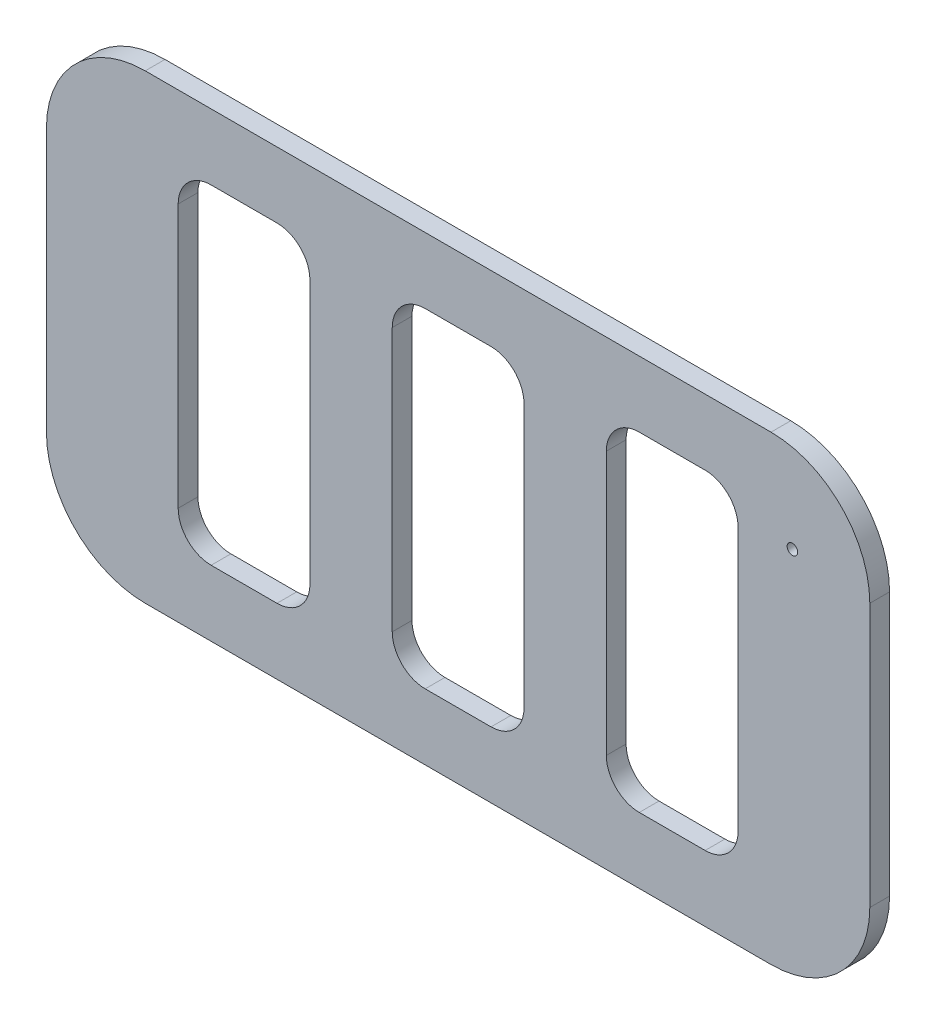
SolidWorks part; units mm, degrees
material "Ferro dúctil"
ref_plane "Plano frontal" through (0, 0, 0) normal (0, 0, 1) x (1, 0, 0)
ref_plane "Plano superior" through (0, 0, 0) normal (0, 1, 0) x (1, 0, 0)
ref_plane "Plano direito" through (0, 0, 0) normal (1, 0, 0) x (0, 0, -1)
sketch "Esboço1" plane through (0, 0, 0) normal (0, 0, 1) x (1, 0, 0)
  line L1 (4.5869, 67.2368) -> (99.5869, 67.2368)
  line L2 (-10.4131, 52.2368) -> (-10.4131, 12.2368)
  line L3 (4.5869, -2.7632) -> (99.5869, -2.7632)
  line L4 (114.5869, 52.2368) -> (114.5869, 12.2368)
  arc A0 (-10.4131, 12.2368) -> (4.5869, -2.7632) centre (4.5869, 12.2368) ccw
  arc A1 (4.5869, 67.2368) -> (-10.4131, 52.2368) centre (4.5869, 52.2368) ccw
  arc A2 (99.5869, 67.2368) -> (114.5869, 52.2368) centre (99.5869, 52.2368) cw
  arc A3 (99.5869, -2.7632) -> (114.5869, 12.2368) centre (99.5869, 12.2368) ccw
  point P6 (-10.4131, -2.7632)
  point P9 (-10.4131, 67.2368)
  point P14 (114.5869, -2.7632)
  dimension "D3" = 15
  dimension "D1" = 70
  dimension "D2" = 125
extrude "Ressalto-extrusão1" add sketch "Esboço1" along normal blind 3
sketch "Esboço2" plane through (0, 0, 0) normal (0, 0, -1) x (-1, 0, 0)
  line L0 (-99.5869, 67.2368) -> (-4.5869, 67.2368) construction
  line L1 (-114.5869, 12.2368) -> (-114.5869, 52.2368) construction
  circle A0 centre (-102.8369, 53.4568) radius 0.8
  dimension "D1" = 1.6
  dimension "D2" = 13.78
  dimension "D3" = 11.75
extrude "Corte-extrusão1" cut sketch "Esboço2" against normal through all
sketch "Esboço3" plane through (0, 0, 0) normal (0, 0, -1) x (-1, 0, 0)
  line L0 (10.4131, 52.2368) -> (10.4131, 12.2368) construction
  line L1 (-14.5869, 7.2368) -> (-24.5869, 7.2368)
  line L2 (-9.5869, 12.2368) -> (-9.5869, 52.2368)
  line L3 (-14.5869, 57.2368) -> (-24.5869, 57.2368)
  line L4 (-29.5869, 12.2368) -> (-29.5869, 52.2368)
  line L5 (-47.0869, 7.2368) -> (-57.0869, 7.2368)
  line L6 (-42.0869, 12.2368) -> (-42.0869, 52.2368)
  line L7 (-47.0869, 57.2368) -> (-57.0869, 57.2368)
  line L8 (-62.0869, 12.2368) -> (-62.0869, 52.2368)
  line L9 (-79.5869, 7.2368) -> (-89.5869, 7.2368)
  line L10 (-74.5869, 12.2368) -> (-74.5869, 52.2368)
  line L11 (-79.5869, 57.2368) -> (-89.5869, 57.2368)
  line L12 (-94.5869, 12.2368) -> (-94.5869, 52.2368)
  line L13 (-114.5869, 12.2368) -> (-114.5869, 52.2368) construction
  line L15 (-99.5869, 67.2368) -> (-4.5869, 67.2368) construction
  arc A0 (-79.5869, 7.2368) -> (-74.5869, 12.2368) centre (-79.5869, 12.2368) ccw
  arc A1 (-89.5869, 7.2368) -> (-94.5869, 12.2368) centre (-89.5869, 12.2368) cw
  arc A2 (-89.5869, 57.2368) -> (-94.5869, 52.2368) centre (-89.5869, 52.2368) ccw
  arc A3 (-74.5869, 52.2368) -> (-79.5869, 57.2368) centre (-79.5869, 52.2368) ccw
  arc A4 (-57.0869, 57.2368) -> (-62.0869, 52.2368) centre (-57.0869, 52.2368) ccw
  arc A5 (-57.0869, 7.2368) -> (-62.0869, 12.2368) centre (-57.0869, 12.2368) cw
  arc A6 (-47.0869, 7.2368) -> (-42.0869, 12.2368) centre (-47.0869, 12.2368) ccw
  arc A7 (-42.0869, 52.2368) -> (-47.0869, 57.2368) centre (-47.0869, 52.2368) ccw
  arc A8 (-24.5869, 57.2368) -> (-29.5869, 52.2368) centre (-24.5869, 52.2368) ccw
  arc A9 (-9.5869, 52.2368) -> (-14.5869, 57.2368) centre (-14.5869, 52.2368) ccw
  arc A10 (-24.5869, 7.2368) -> (-29.5869, 12.2368) centre (-24.5869, 12.2368) cw
  arc A11 (-14.5869, 7.2368) -> (-9.5869, 12.2368) centre (-14.5869, 12.2368) ccw
  point P18 (-74.5869, 7.2368)
  point P21 (-94.5869, 7.2368)
  point P30 (-62.0869, 7.2368)
  point P33 (-42.0869, 7.2368)
  point P42 (-29.5869, 7.2368)
  point P45 (-9.5869, 7.2368)
  dimension "D8" = 5
  dimension "D1" = 20
  dimension "D2" = 20
  dimension "D3" = 20
  dimension "D4" = 20
  dimension "D5" = 20
  dimension "D6" = 12.5
  dimension "D7" = 50
  dimension "D9" = 50
  dimension "D10" = 50
  dimension "D11" = 10
  dimension "D12" = 10
  dimension "D13" = 10
extrude "Corte-extrusão2" cut sketch "Esboço3" against normal blind 10
